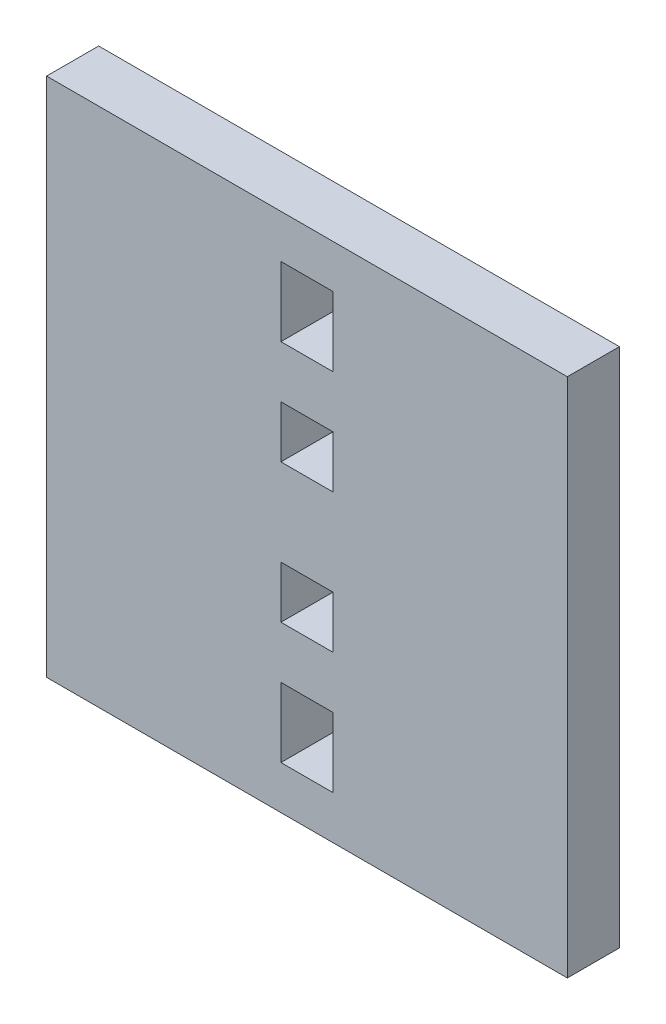
SolidWorks part; units mm, degrees
ref_plane "Front Plane" through (0, 0, 0) normal (0, 0, 1) x (1, 0, 0)
ref_plane "Top Plane" through (0, 0, 0) normal (0, 1, 0) x (1, 0, 0)
ref_plane "Right Plane" through (0, 0, 0) normal (1, 0, 0) x (0, 0, -1)
sketch "Sketch2" plane through (0, 0, 0) normal (0, 0, 1) x (1, 0, 0)
  line L0 (-42.9445, 7.4757) -> (44.1526, 7.4757) construction
  line L1 (-30, 37.4757) -> (30, 37.4757)
  line L2 (-30, 37.4757) -> (-30, -22.5243)
  line L3 (-30, -22.5243) -> (30, -22.5243)
  line L4 (30, 37.4757) -> (30, -22.5243)
  line L5 (0, 42.672) -> (0, -26.6728) construction
  line L6 (-3, -9.5243) -> (-3, -17.5243)
  line L9 (3, 2.4757) -> (-3, 2.4757)
  line L10 (3, 2.4757) -> (3, -3.5243)
  line L11 (3, -3.5243) -> (-3, -3.5243)
  line L12 (-3, 2.4757) -> (-3, -3.5243)
  line L15 (-3, -9.5243) -> (3, -9.5243)
  line L17 (-3, -17.5243) -> (3, -17.5243)
  line L18 (3, -9.5243) -> (3, -17.5243)
  line L22 (3, 24.4757) -> (3, 32.4757)
  line L24 (-3, 32.4757) -> (3, 32.4757)
  line L25 (-3, 24.4757) -> (-3, 32.4757)
  line L26 (-3, 24.4757) -> (3, 24.4757)
  line L28 (3, 18.4757) -> (-3, 18.4757)
  line L29 (3, 12.4757) -> (3, 18.4757)
  line L31 (3, 12.4757) -> (-3, 12.4757)
  line L32 (-3, 12.4757) -> (-3, 18.4757)
  point P9 (0, 7.4757)
  dimension "D1" = 30
  dimension "D2" = 30
  dimension "D3" = 30
  dimension "D4" = 30
  dimension "D5" = 3
  dimension "D7" = 5
  dimension "D8" = 6
  dimension "D9" = 6
  dimension "D10" = 8
  dimension "D12" = 6
extrude "Boss-Extrude1" add sketch "Sketch2" along normal blind 6
